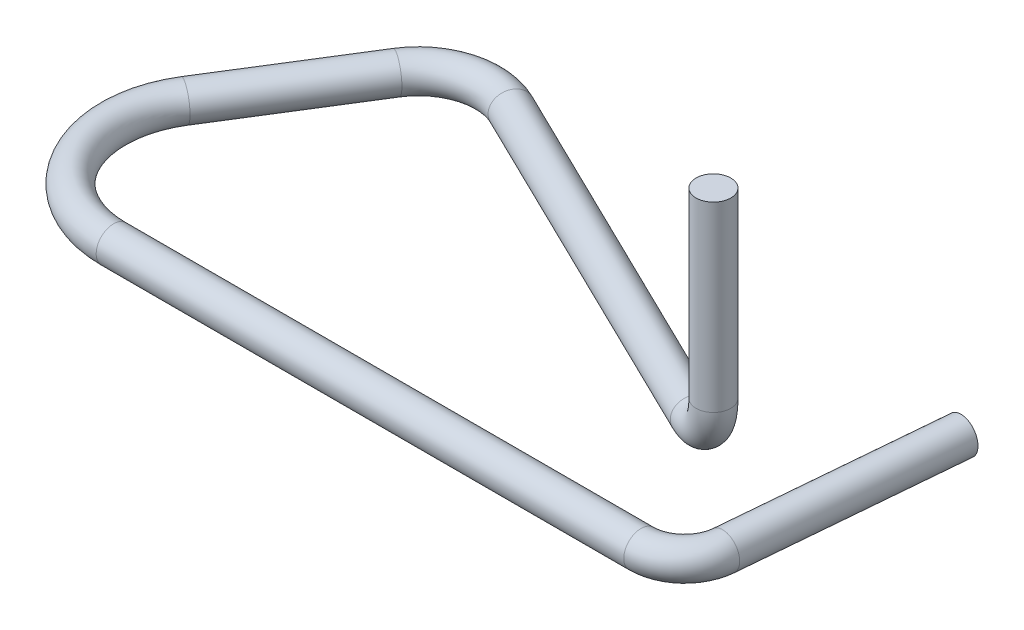
SolidWorks part; units mm, degrees
ref_plane "Front" through (0, 0, 0) normal (0, 0, 1) x (1, 0, 0)
ref_plane "Top" through (0, 0, 0) normal (0, 1, 0) x (1, 0, 0)
ref_plane "Right" through (0, 0, 0) normal (1, 0, 0) x (0, 0, -1)
sketch "Sketch1" plane through (0, 0, 0) normal (0, 1, 0) x (1, 0, 0)
  line L0 (19.0034, 0.508) -> (3.556, 0.508)
  line L1 (0.9711, 5.1712) -> (3.3568, 8.989)
  line L2 (5.9708, 9.7385) -> (17.526, 4.1027) construction
  line L3 (0.508, 3.556) -> (0.508, 0.7447) construction
  line L4 (0.508, 3.556) -> (0.508, 7.7927) construction
  line L5 (20.2686, 1.6673) -> (20.8299, 8.0837)
  line L6 (20.3239, 8.128) -> (21.336, 8.0394) construction
  line L7 (5.9708, 9.7385) -> (16.3845, 4.6594)
  arc A0 (3.556, 0.508) -> (0.9711, 5.1712) centre (3.556, 3.556) cw
  arc A1 (3.3568, 8.989) -> (5.9708, 9.7385) centre (5.08, 7.9122) cw
  arc A2 (20.2686, 1.6673) -> (19.0034, 0.508) centre (19.0034, 1.778) cw
  point P17 (20.8299, 8.0837)
  dimension "D2" = 3.048
  dimension "D5" = 2.032
  dimension "D10" = 1.27
  dimension "D1" = 0.508
  dimension "D3" = 0.508
  dimension "D4" = 32
  dimension "D6" = 96
  dimension "D7" = 4.572
  dimension "D8" = 7.9122
  dimension "D9" = 95
  dimension "D11" = 1.016
  dimension "D12" = 8.128
  dimension "D13" = 20.828
  dimension "D14" = 17.018
  dimension "D15" = 1.27
ref_plane "Plane1" through (17.526, 0, 0) normal (1, 0, 0) x (0, 0, -1)
sketch "Sketch2" plane through (17.526, 0, 0) normal (1, 0, 0) x (0, 0, -1)
  line L0 (4.1027, 0) -> (4.1027, 6.604) construction
  dimension "D1" = 6.604
ref_plane "Plane2" through (4.9844, 0, -10.2196) normal (0.4384, 0, -0.8988) x (-0.8988, 0, -0.4384)
sketch "Sketch3" plane through (4.9844, 0, -10.2196) normal (0.4384, 0, -0.8988) x (-0.8988, 0, -0.4384)
  line L0 (-13.9538, 6.604) -> (-13.9538, 1.27)
  line L1 (-1.0974, 0) -> (-12.6838, 0) construction
  line L2 (-13.9538, 0) -> (-13.9538, 6.604) construction
  line L3 (-1.0974, 0) -> (-12.6838, 0) construction
  arc A0 (-13.9538, 1.27) -> (-12.6838, 0) centre (-12.6838, 1.27) ccw
ref_plane "Plane3" through (0, 6.604, 0) normal (0, 1, 0) x (1, 0, 0)
sketch "Sketch4" plane through (0, 6.604, 0) normal (0, 1, 0) x (1, 0, 0)
  circle A0 centre (17.526, 4.1027) radius 0.508
  dimension "D1" = 1.016
curve "CompCurve1"
sweep "Sweep1" add profiles "Sketch4" path "CompCurve1"
